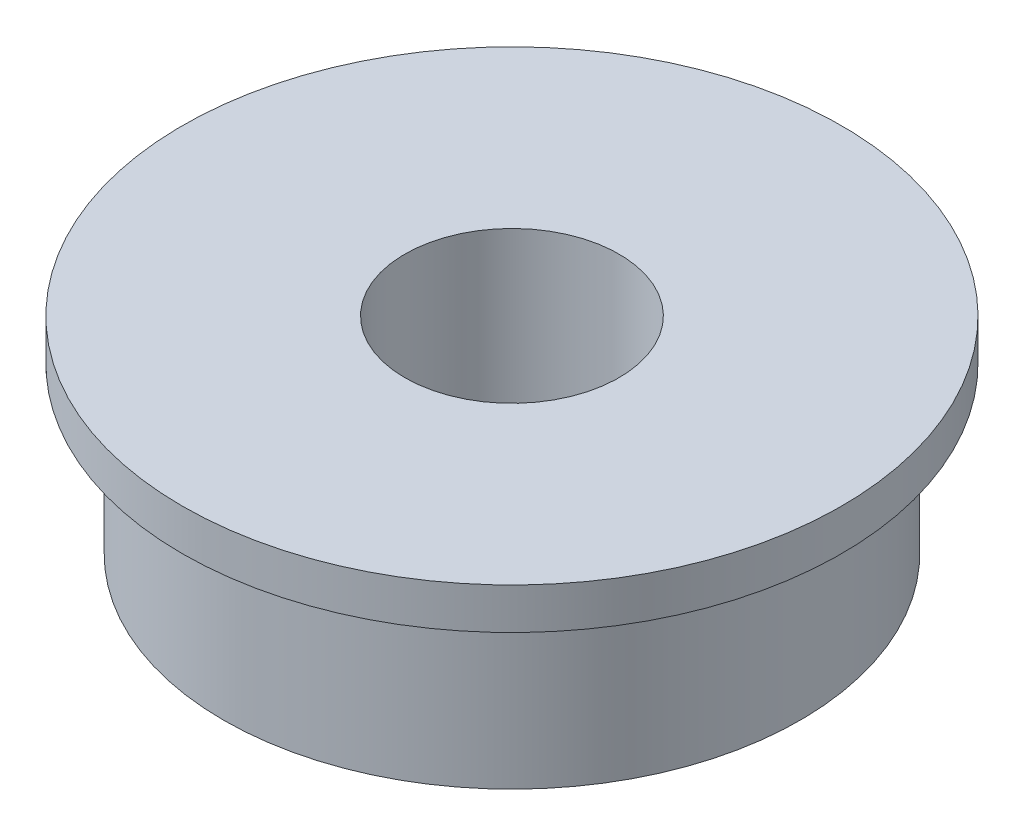
SolidWorks part; units mm, degrees
material "1023 碳钢板 (SS)"
ref_plane "前视基准面" through (0, 0, 0) normal (0, 0, 1) x (1, 0, 0)
ref_plane "上视基准面" through (0, 0, 0) normal (0, 1, 0) x (1, 0, 0)
ref_plane "右视基准面" through (0, 0, 0) normal (1, 0, 0) x (0, 0, -1)
sketch "草图1" plane through (0, 0, 0) normal (0, 1, 0) x (1, 0, 0)
  circle A0 centre (0, 0) radius 2.6
  circle A1 centre (0, 0) radius 7
  dimension "D1" = 5.2
  dimension "D2" = 14
extrude "凸台-拉伸1" add sketch "草图1" along normal blind 5
sketch "草图2" plane through (0, 5, 0) normal (0, 1, 0) x (1, 0, 0)
  circle A0 centre (0, 0) radius 2.6
  circle A1 centre (0, 0) radius 8
  circle A2 centre (0, 0) radius 2.6 construction
  dimension "D1" = 16
extrude "凸台-拉伸2" add sketch "草图2" against normal blind 1
